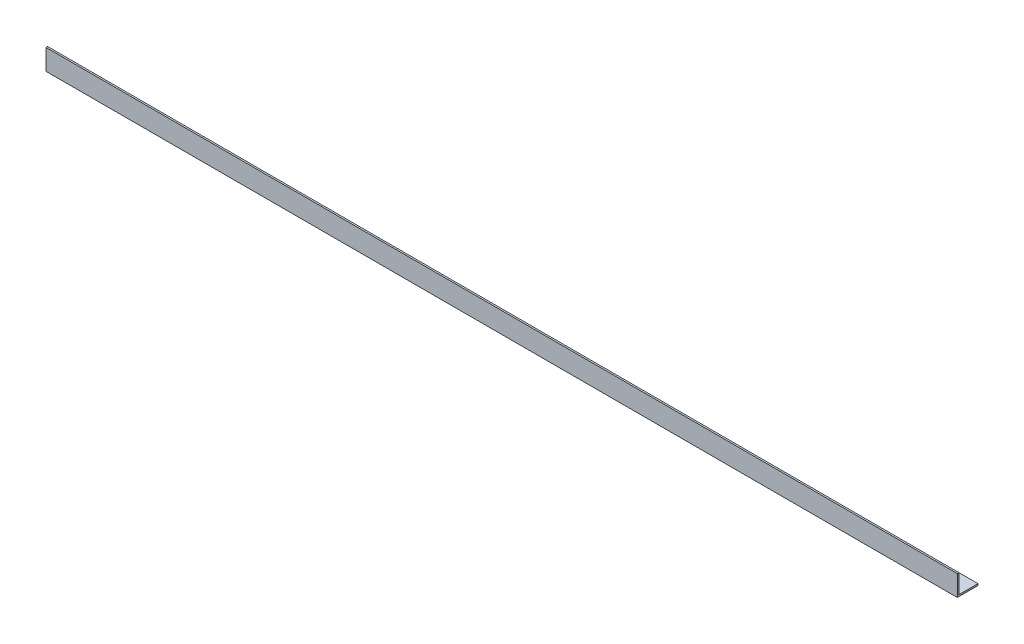
SolidWorks part; units mm, degrees
ref_plane "Спереди" through (0, 0, 0) normal (0, 0, 1) x (1, 0, 0)
ref_plane "Сверху" through (0, 0, 0) normal (0, 1, 0) x (1, 0, 0)
ref_plane "Справа" through (0, 0, 0) normal (1, 0, 0) x (0, 0, -1)
sketch "Эскиз1" plane through (0, 0, 0) normal (1, 0, 0) x (0, 0, -1)
  line L0 (0, 37.7) -> (0, 0)
  line L1 (0, 0) -> (37.7, 0)
extrude "Вытянуть-Тонкостенный1" add sketch "Эскиз1" along normal blind 1660 thin thin type one direction reverse wall 3
